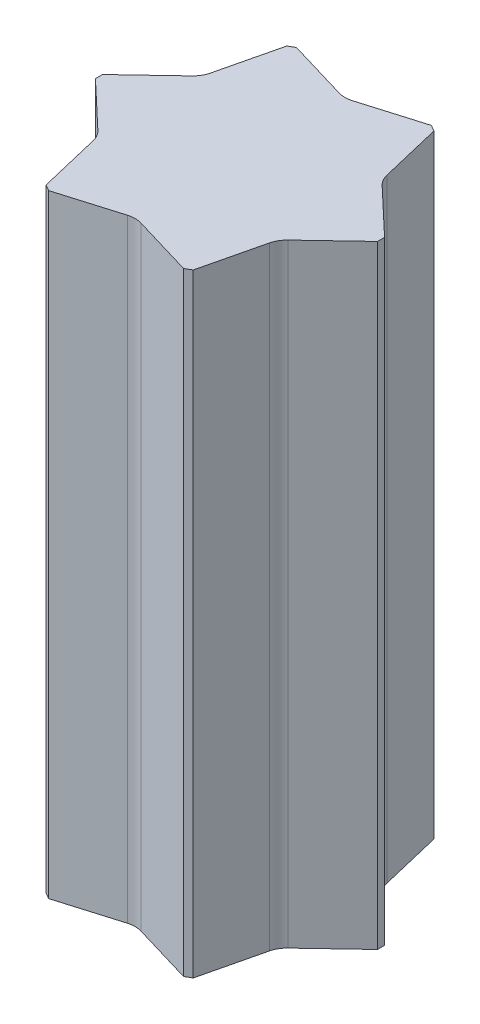
SolidWorks part; units mm, degrees
material "PEN"
ref_plane "前视基准面" through (0, 0, 0) normal (0, 0, 1) x (1, 0, 0)
ref_plane "上视基准面" through (0, 0, 0) normal (0, 1, 0) x (1, 0, 0)
ref_plane "右视基准面" through (0, 0, 0) normal (1, 0, 0) x (0, 0, -1)
sketch "草图2" plane through (0, 0, 0) normal (0, 1, 0) x (1, 0, 0)
  line L1 (345, 8.6603) -> (180, 294.4486)
  line L2 (165, 303.1089) -> (-165, 303.1089)
  line L3 (-180, 294.4486) -> (-345, 8.6603)
  line L4 (-345, -8.6603) -> (-180, -294.4486)
  line L5 (-165, -303.1089) -> (165, -303.1089)
  line L6 (180, -294.4486) -> (345, -8.6603)
  line L8 (-180, 294.4486) -> (-165, 303.1089)
  line L19 (165, 303.1089) -> (180, 294.4486)
  line L20 (345, 8.6603) -> (345, -8.6603)
  line L21 (165, -303.1089) -> (180, -294.4486)
  line L22 (-180, -294.4486) -> (-165, -303.1089)
  line L23 (-345, 8.6603) -> (-345, -8.6603)
  circle A0 centre (0, 0) radius 303.1089 construction
extrude "凸台-拉伸1" add sketch "草图2" along normal blind 1500
sketch "草图4" plane through (0, 0, 0) normal (0, 1, 0) x (1, 0, 0)
  line L1 (165, 303.1089) -> (-165, 303.1089) construction
  line L3 (-165, 313.5155) -> (-16.245, 357.745)
  line L4 (165, 292.7023) -> (16.245, 248.4728)
  line L5 (165, 313.5155) -> (16.245, 357.745)
  line L6 (-165, 292.7023) -> (-16.245, 248.4728)
  line L7 (-165, 303.1089) -> (-165, 313.5155)
  line L8 (-165, 303.1089) -> (-165, 292.7023)
  line L9 (165, 303.1089) -> (165, 313.5155)
  line L10 (165, 303.1089) -> (165, 292.7023)
  arc A0 (-16.245, 248.4728) -> (16.245, 248.4728) centre (0, 303.1089) ccw
  arc A1 (16.245, 357.745) -> (-16.245, 357.745) centre (0, 303.1089) ccw
sketch "草图5" plane through (0, 0, 0) normal (0, 1, 0) x (1, 0, 0)
  line L0 (165, 303.1089) -> (16.2451, 258.8793)
  line L1 (198.0248, 304.8553) -> (310.7062, 198.1444)
  line L2 (180, 294.4486) -> (198.0248, 304.8553)
  line L3 (-165, 303.1089) -> (-16.2451, 258.8793)
  line L4 (-165, 323.9221) -> (-16.245, 368.1516)
  line L5 (165, 323.9221) -> (16.245, 368.1516)
  line L6 (-165, 303.1089) -> (-165, 323.9221)
  line L7 (165, 303.1089) -> (165, 323.9221)
  line L8 (180, 294.4486) -> (216.0735, 143.5083)
  line L9 (345, 8.6603) -> (232.3186, 115.371)
  line L10 (345, 8.6603) -> (363.0248, 19.0669)
  line L11 (363.0248, 19.0669) -> (326.9512, 170.0072)
  line L12 (363.0248, -19.0669) -> (326.9512, -170.0072)
  line L13 (345, -8.6603) -> (363.0248, -19.0669)
  line L14 (345, -8.6603) -> (232.3186, -115.371)
  line L15 (180, -294.4486) -> (216.0735, -143.5083)
  line L16 (180, -294.4486) -> (198.0248, -304.8553)
  line L17 (198.0248, -304.8553) -> (310.7062, -198.1444)
  line L18 (165, -323.9221) -> (16.245, -368.1516)
  line L19 (165, -303.1089) -> (165, -323.9221)
  line L20 (165, -303.1089) -> (16.2451, -258.8793)
  line L21 (-165, -303.1089) -> (-16.2451, -258.8793)
  line L22 (-165, -303.1089) -> (-165, -323.9221)
  line L23 (-165, -323.9221) -> (-16.245, -368.1516)
  line L24 (-198.0248, -304.8553) -> (-310.7062, -198.1444)
  line L25 (-180, -294.4486) -> (-198.0248, -304.8553)
  line L26 (-180, -294.4486) -> (-216.0735, -143.5083)
  line L27 (-345, -8.6603) -> (-232.3186, -115.371)
  line L28 (-345, -8.6603) -> (-363.0248, -19.0669)
  line L29 (-363.0248, -19.0669) -> (-326.9512, -170.0072)
  line L30 (-363.0248, 19.0669) -> (-326.9512, 170.0072)
  line L31 (-345, 8.6603) -> (-363.0248, 19.0669)
  line L32 (-345, 8.6603) -> (-232.3186, 115.371)
  line L33 (-180, 294.4486) -> (-216.0735, 143.5083)
  line L34 (-180, 294.4486) -> (-198.0248, 304.8553)
  line L35 (-198.0248, 304.8553) -> (-310.7062, 198.1444)
  arc A0 (-16.2451, 258.8793) -> (16.2451, 258.8793) centre (0, 313.5155) ccw
  arc A1 (16.245, 368.1516) -> (-16.245, 368.1516) centre (0, 313.5155) ccw
  arc A2 (326.9512, 170.0072) -> (310.7062, 198.1444) centre (271.5124, 156.7577) ccw
  arc A3 (216.0735, 143.5083) -> (232.3186, 115.371) centre (271.5124, 156.7577) ccw
  arc A4 (310.7062, -198.1444) -> (326.9512, -170.0072) centre (271.5124, -156.7577) ccw
  arc A5 (232.3186, -115.371) -> (216.0735, -143.5083) centre (271.5124, -156.7577) ccw
  arc A6 (-16.245, -368.1516) -> (16.245, -368.1516) centre (0, -313.5155) ccw
  arc A7 (16.2451, -258.8793) -> (-16.2451, -258.8793) centre (0, -313.5155) ccw
  arc A8 (-326.9512, -170.0072) -> (-310.7062, -198.1444) centre (-271.5124, -156.7577) ccw
  arc A9 (-216.0735, -143.5083) -> (-232.3186, -115.371) centre (-271.5124, -156.7577) ccw
  arc A10 (-310.7062, 198.1444) -> (-326.9512, 170.0072) centre (-271.5124, 156.7577) ccw
  arc A11 (-232.3186, 115.371) -> (-216.0735, 143.5083) centre (-271.5124, 156.7577) ccw
  dimension "D1" = 6
extrude "切除-拉伸4" cut sketch "草图5" along normal blind 1500
shell "抽壳3" thickness 10
sketch "草图6" plane through (0, 0, 0) normal (0, 0, 1) x (1, 0, 0)
  line L0 (0, 0) -> (0, 1500)
  line L1 (303.1089, 0) -> (-303.1089, 0) construction
  line L2 (16.2451, 1500) -> (-16.2451, 1500) construction
